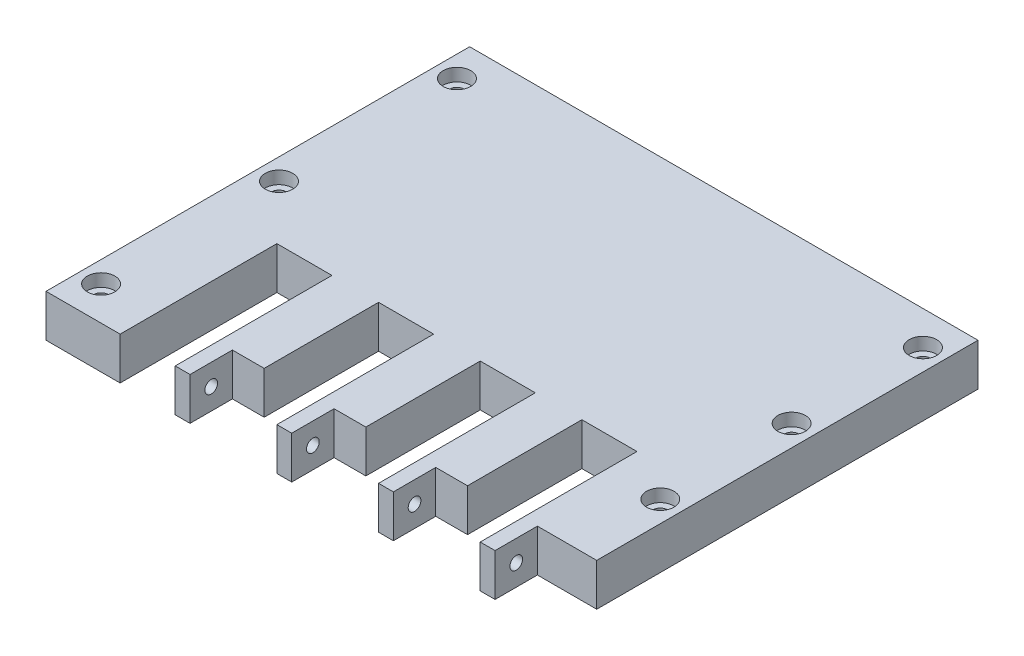
SolidWorks part; units mm, degrees
material "Plain Carbon Steel"
ref_plane "Front Plane" through (0, 0, 0) normal (0, 0, 1) x (1, 0, 0)
ref_plane "Top Plane" through (0, 0, 0) normal (0, 1, 0) x (1, 0, 0)
ref_plane "Right Plane" through (0, 0, 0) normal (1, 0, 0) x (0, 0, -1)
sketch "Sketch1" plane through (0, 0, 0) normal (0, 1, 0) x (1, 0, 0)
  line L1 (60, -50) -> (-60, -50)
  line L2 (60, -50) -> (60, 50)
  line L3 (60, 50) -> (-60, 50)
  line L4 (-60, -50) -> (-60, 50)
  line L5 (60, -50) -> (-60, 50) construction
  line L6 (60, 50) -> (-60, -50) construction
  point P0 (0, 0)
  dimension "D1" = 120
  dimension "D2" = 100
extrude "Boss-Extrude1" add sketch "Sketch1" along normal blind 10
sketch "Sketch2" plane through (0, 0, 50) normal (0, 0, 1) x (1, 0, 0)
  line L0 (-60, 0) -> (60, 0) construction
  line L1 (60, 10) -> (-60, 10) construction
  line L4 (-29.5, -10) -> (-42.5, -10)
  line L5 (-29.5, -10) -> (-29.5, 10)
  line L6 (-29.5, 10) -> (-42.5, 10)
  line L7 (-42.5, -10) -> (-42.5, 10)
  line L8 (-29.5, -10) -> (-42.5, 10) construction
  line L9 (-29.5, 10) -> (-42.5, -10) construction
  line L10 (-5.5, -10) -> (-18.5, -10)
  line L11 (-5.5, -10) -> (-5.5, 10)
  line L12 (-5.5, 10) -> (-18.5, 10)
  line L13 (-18.5, -10) -> (-18.5, 10)
  line L14 (-5.5, -10) -> (-18.5, 10) construction
  line L15 (-5.5, 10) -> (-18.5, -10) construction
  line L16 (18.5, -10) -> (5.5, -10)
  line L17 (18.5, -10) -> (18.5, 10)
  line L18 (18.5, 10) -> (5.5, 10)
  line L19 (5.5, -10) -> (5.5, 10)
  line L20 (18.5, -10) -> (5.5, 10) construction
  line L21 (18.5, 10) -> (5.5, -10) construction
  line L22 (42.5, -10) -> (29.5, -10)
  line L23 (42.5, -10) -> (42.5, 10)
  line L24 (42.5, 10) -> (29.5, 10)
  line L25 (29.5, -10) -> (29.5, 10)
  line L26 (42.5, -10) -> (29.5, 10) construction
  line L27 (42.5, 10) -> (29.5, -10) construction
  line L29 (60, 0) -> (-60, 0) construction
  point P7 (-36, 0)
  point P8 (-12, 0)
  point P9 (12, 0)
  point P10 (36, 0)
  point P11 (-36, 0)
  point P16 (-12, 0)
  point P21 (12, 0)
  point P26 (36, 0)
  point P33 (0, 0)
  dimension "D1" = 120
  dimension "D3" = 13
extrude "Cut-Extrude1" cut sketch "Sketch2" against normal blind 37
sketch "Sketch3" plane through (0, 0, 50) normal (0, 0, 1) x (1, 0, 0)
  line L0 (60, 10) -> (60, 0) construction
  line L1 (-18.5, 0) -> (-26, 0)
  line L2 (-18.5, 0) -> (-18.5, 10)
  line L3 (-18.5, 10) -> (-26, 10)
  line L4 (-26, 0) -> (-26, 10)
  line L5 (5.5, 0) -> (-2, 0)
  line L6 (5.5, 0) -> (5.5, 10)
  line L7 (5.5, 10) -> (-2, 10)
  line L8 (-2, 0) -> (-2, 10)
  line L9 (29.5, 0) -> (22, 0)
  line L10 (29.5, 0) -> (29.5, 10)
  line L11 (29.5, 10) -> (22, 10)
  line L12 (22, 0) -> (22, 10)
  line L13 (46, 0) -> (60, 0)
  line L14 (46, 0) -> (46, 10)
  line L15 (46, 10) -> (60, 10)
  line L16 (60, 0) -> (60, 10)
  line L17 (60, 0) -> (42.5, 0) construction
  line L18 (5.5, 10) -> (5.5, 0) construction
  line L19 (5.5, 0) -> (-5.5, 0) construction
  line L21 (-29.5, 0) -> (-29.5, 10) construction
  line L22 (-5.5, 0) -> (-5.5, 10) construction
  line L23 (42.5, 0) -> (42.5, 10) construction
  line L24 (18.5, 0) -> (18.5, 10) construction
  line L25 (-18.5, 0) -> (-5.5, 0) construction
  line L26 (-18.5, 10) -> (-18.5, 0) construction
  line L29 (-18.5, 10) -> (-29.5, 10) construction
  line L33 (5.5, 10) -> (-5.5, 10) construction
  line L34 (29.5, 10) -> (18.5, 10) construction
  line L35 (60, 10) -> (42.5, 10) construction
  dimension "D1" = 3.5
  dimension "D2" = 3.5
  dimension "D3" = 3.5
  dimension "D4" = 3.5
extrude "Cut-Extrude4" cut sketch "Sketch3" against normal blind 10 contours L13 L16 L15 L14 | L10 L9 L12 L11 | L6 L5 L8 L7 | L2 L1 L4 L3
sketch "Sketch10" plane through (46, 0, 0) normal (1, 0, 0) x (0, 0, -1)
  line L0 (-40, 0) -> (-50, 0) construction
  line L1 (-50, 0) -> (-50, 10) construction
  circle A0 centre (-45, 5) radius 1.5
  dimension "D1" = 3
  dimension "D2" = 5
  dimension "D3" = 5
extrude "Cut-Extrude5" cut sketch "Sketch10" against normal up to surface (75.5 mm away) up to face at (-29.5, 5, 31.5)
hole_wizard "CBORE for M3 SHCS" positions "Sketch7" profile "Sketch8" counterbore size "M3" standard "ANSI Metric"
sketch "Sketch7" plane through (-676.2935, 10, -1323.2827) normal (0, 1, 0) x (1, 0, 0)
  line L3 (621.2935, -1281.2827) -> (621.2935, -1365.2827) construction
  line L5 (731.2935, -1281.2827) -> (731.2935, -1343.2827) construction
  circle A0 centre (731.2935, -1281.2827) radius 2.243
  circle A1 centre (731.2935, -1343.2827) radius 2.2384
  circle A3 centre (621.2935, -1281.2827) radius 2.3325
  circle A4 centre (621.2935, -1365.2827) radius 1.7576
  circle A5 centre (621.2935, -1323.2827) radius 1.8624
  circle A6 centre (731.2935, -1312.2827) radius 2.0271
  point P1 (731.2935, -1281.2827)
  point P8 (731.2935, -1343.2827)
  point P15 (621.2935, -1281.2827)
  point P17 (621.2935, -1365.2827)
  point P19 (621.2935, -1323.2827)
  point P27 (731.2935, -1312.2827)
sketch "Sketch8" plane through (55, 10, -42) normal (1, 0, 0) x (0, 0, 1)
  line L0 (0, 0) -> (0, 24.0215)
  line L1 (0, 24.0215) -> (1.7, 23)
  line L2 (1.7, 23) -> (1.7, 3)
  line L3 (1.7, 3) -> (3.25, 3)
  line L4 (3.25, 3) -> (3.25, 0)
  line L5 (3.25, 0) -> (0, 0)
  line L6 (0, 24.0215) -> (-1.7, 23) construction
  line L7 (0, -6.35) -> (0, 107.95) construction
  dimension "Hole Dia." = 3.4
  dimension "Hole Depth" = 23
  dimension "C'Bore Dia." = 6.5
  dimension "C'Bore Depth" = 3
  dimension "Drill Angle" = 118
